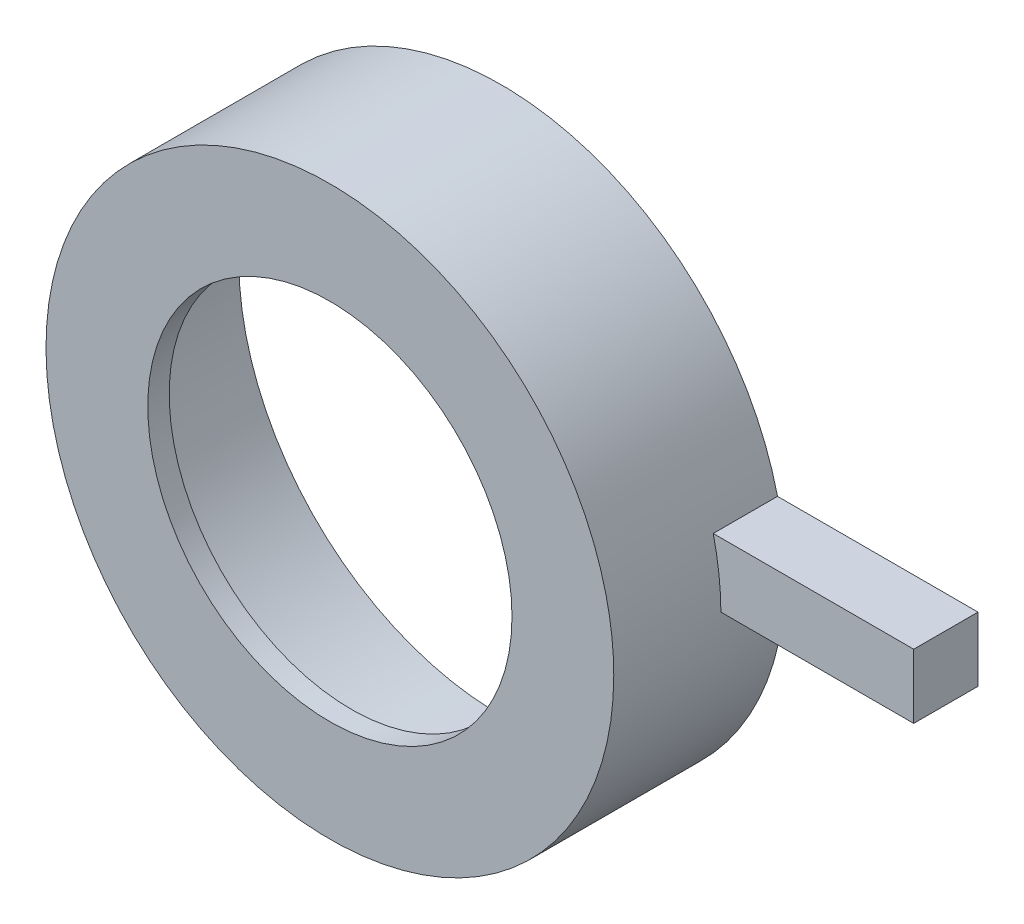
SolidWorks part; units mm, degrees
ref_plane "正面" through (0, 0, 0) normal (0, 0, 1) x (1, 0, 0)
ref_plane "平面" through (0, 0, 0) normal (0, 1, 0) x (1, 0, 0)
ref_plane "右側面" through (0, 0, 0) normal (1, 0, 0) x (0, 0, -1)
sketch "ｽｹｯﾁ1" plane through (0, 0, 0) normal (0, 0, 1) x (1, 0, 0)
  circle A0 centre (0, 0) radius 12.25
  circle A1 centre (0, 0) radius 13.25
  dimension "D1" = 24.5
  dimension "D2" = 26.5
extrude "ﾎﾞｽ - 押し出し1" add sketch "ｽｹｯﾁ1" along normal blind 7
sketch "ｽｹｯﾁ2" plane through (0, 0, 7) normal (0, 0, 1) x (1, 0, 0)
  circle A0 centre (0, 0) radius 13.25
  circle A1 centre (0, 0) radius 8.5
  dimension "D1" = 17
extrude "ﾎﾞｽ - 押し出し2" add sketch "ｽｹｯﾁ2" along normal blind 1
sketch "ｽｹｯﾁ3" plane through (0, 0, 0) normal (0, 0, 1) x (1, 0, 0)
  line L1 (12.25, 3.0569) -> (22.25, 3.0569)
  line L2 (12.25, 3.0569) -> (12.25, 0.0569)
  line L3 (12.25, 0.0569) -> (22.25, 0.0569)
  line L4 (22.25, 3.0569) -> (22.25, 0.0569)
  dimension "D1" = 10
  dimension "D2" = 3
extrude "ﾎﾞｽ - 押し出し3" add sketch "ｽｹｯﾁ3" along normal blind 3
